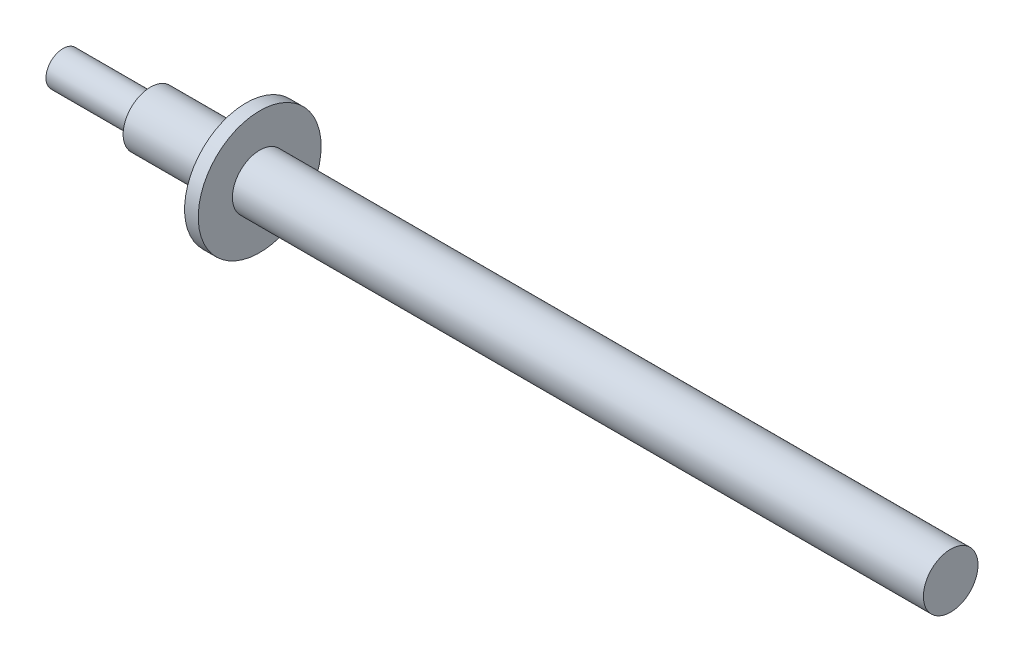
SolidWorks part; units mm, degrees
material "1023 Carbon Steel Sheet (SS)"
ref_plane "Front Plane" through (0, 0, 0) normal (0, 0, 1) x (1, 0, 0)
ref_plane "Top Plane" through (0, 0, 0) normal (0, 1, 0) x (1, 0, 0)
ref_plane "Right Plane" through (0, 0, 0) normal (1, 0, 0) x (0, 0, -1)
ref_plane "Right Plane1" through (13.4, 0, 0) normal (1, 0, 0) x (0, 0, -1)
sketch "Sketch1" plane through (0, 0, 0) normal (1, 0, 0) x (0, 0, -1)
  circle A0 centre (0, 0) radius 2
  dimension "D1" = 4
extrude "Boss-Extrude1" add sketch "Sketch1" along normal blind 65
sketch "Sketch2" plane through (13.4, 0, 0) normal (1, 0, 0) x (0, 0, -1)
  circle A0 centre (0, 0) radius 4.5
  dimension "D1" = 9
extrude "Boss-Extrude2" add sketch "Sketch2" along normal blind 1
sketch "Sketch3" plane through (0, 0, 0) normal (1, 0, 0) x (0, 0, -1)
  circle A0 centre (0, 0) radius 2
  circle A1 centre (0, 0) radius 1.25
  dimension "D1" = 2.5
  dimension "D2" = 4
extrude "Cut-Extrude1" cut sketch "Sketch3" along normal blind 6.4
sketch "Sketch4" plane through (0, 0, 0) normal (0, 1, 0) x (1, 0, 0)
  line L0 (0, 0) -> (65, 0) construction
  line L1 (65, -2) -> (65, 2) construction
